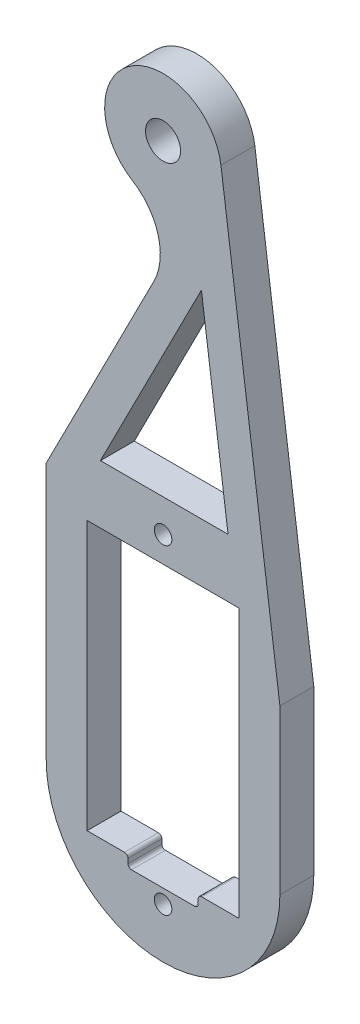
SolidWorks part; units mm, degrees
material "普通碳钢"
ref_plane "前视基准面" through (0, 0, 0) normal (0, 0, 1) x (1, 0, 0)
ref_plane "上视基准面" through (0, 0, 0) normal (0, 1, 0) x (1, 0, 0)
ref_plane "右视基准面" through (0, 0, 0) normal (1, 0, 0) x (0, 0, -1)
sketch "草图1" plane through (0, 0, 0) normal (0, 0, 1) x (1, 0, 0)
  line L0 (0, 0) -> (18.9934, 0) construction
  line L1 (-6.5, 11.5) -> (6.5, 11.5)
  line L2 (-6.5, 11.5) -> (-6.5, -11.5)
  line L3 (-6.5, -11.5) -> (6.5, -11.5)
  line L4 (6.5, 11.5) -> (6.5, -11.5)
  line L5 (-6.5, 11.5) -> (6.5, -11.5) construction
  line L6 (-6.5, -11.5) -> (6.5, 11.5) construction
  line L7 (0, 0) -> (0, 13.7) construction
  line L8 (0, -8) -> (0, 0) construction
  line L9 (0, 42.88) -> (0, 0) construction
  line L10 (10, -8) -> (10, 6)
  line L11 (10, 6) -> (4.9555, 43.5458)
  line L12 (-10, -8) -> (-10, 14)
  line L13 (-10, 14) -> (-0.7821, 32.0911)
  line L14 (-5.3592, 16.5) -> (3.2833, 33.462)
  line L15 (5.5623, 16.5) -> (3.2833, 33.462)
  line L16 (-7.327, 12.638) -> (1.8909, 30.7291) construction
  line L17 (7.0267, 5.6005) -> (1.9822, 43.1463) construction
  line L18 (-5.3592, 16.5) -> (5.5623, 16.5)
  line L19 (-6.5, 16.5) -> (6.5, 16.5) construction
  circle A0 centre (0, 13.7) radius 0.75
  circle A1 centre (0, -13.7) radius 0.75
  arc A2 (-10, -8) -> (10, -8) centre (0, -8) ccw
  arc A3 (4.9555, 43.5458) -> (0, 37.88) centre (0, 42.88) ccw
  circle A4 centre (0, -5.12) radius 4 construction
  arc A5 (-0.7821, 32.0911) -> (-2.6186, 38.6205) centre (-5.2372, 34.3611) ccw
  circle A6 centre (0, 42.88) radius 1.5
  point P0 (0, 0)
  dimension "D3" = 1.5
  dimension "D5" = 10
  dimension "D7" = 10
  dimension "D10" = 8
  dimension "D13" = 10
  dimension "D14" = 63
  dimension "D18" = 3
  dimension "D1" = 23
  dimension "D2" = 13
  dimension "D4" = 27.4
  dimension "D6" = 8
  dimension "D8" = 6.38
  dimension "D9" = 48
  dimension "D11" = 14
  dimension "D12" = 22
  dimension "D15" = 3
  dimension "D16" = 3
  dimension "D17" = 5
extrude "凸台-拉伸1" add sketch "草图1" along normal mid plane 2.9
sketch "草图2" plane through (0, 0, 1.45) normal (0, 0, 1) x (1, 0, 0)
  line L0 (-3, -11.5) -> (-3, -12.5)
  line L1 (-6.5, -11.5) -> (6.5, -11.5) construction
  line L2 (-3, -12.5) -> (3, -12.5)
  line L3 (3, -12.5) -> (3, -11.5)
  line L4 (0, -11.5) -> (0, -9.1202) construction
  line L5 (3, -11.5) -> (-3, -11.5)
  dimension "D1" = 6
  dimension "D2" = 1
extrude "切除-拉伸1" cut sketch "草图2" against normal blind 3
fillet "圆角1" radius 0.3 4 edges at (3, -12.5, 0) (3, -11.5, 0) (-3, -12.5, 0) (-3, -11.5, 0)
ref_plane "基准面1" through (0, 0, 15.1) normal (0, 0, 1) x (1, 0, 0)
sketch "草图3" plane through (0, 0, 15.1) normal (0, 0, 1) x (1, 0, 0)
  line L1 (0, 0) -> (0, -5.12) construction
  line L2 (0, -5.12) -> (0, -23.7534) construction
  line L4 (0, 42.88) -> (0, 23.9443) construction
  line L5 (0, 42.88) -> (14.4676, 42.88) construction
  line L6 (0, 42.88) -> (-12.4617, 42.88) construction
  line L7 (0, 42.88) -> (0, 55.3705) construction
  line L8 (0, -5.12) -> (20.2751, -5.12) construction
  line L9 (0, -5.12) -> (-32.8736, -5.12) construction
  arc A1 (-10, -8) -> (10, -8) centre (0, -8) ccw construction
  dimension "D1" = 2.88
ref_plane "基准面2" through (0, 0, -15.1) normal (0, 0, -1) x (-1, 0, 0)
sketch "草图4" plane through (0, 0, -15.1) normal (0, 0, -1) x (-1, 0, 0)
  line L0 (0, 0) -> (0, -5.12) construction
  line L3 (0, -5.12) -> (-20.2751, -5.12) construction
  line L4 (0, 42.88) -> (0, 24.0552) construction
  line L5 (0, 42.88) -> (0, 58.3283) construction
  line L6 (0, 42.88) -> (-19.9233, 42.88) construction
  line L7 (0, 42.88) -> (17.1367, 42.88) construction
  line L8 (0, -5.12) -> (0, -23.7534) construction
  line L9 (0, -5.12) -> (32.8736, -5.12) construction
  line L10 (0, 0) -> (0, -5.12)
  line L11 (0, -5.12) -> (-20.2751, -5.12)
  line L12 (0, -5.12) -> (0, -23.7534)
  line L13 (0, -5.12) -> (32.8736, -5.12)
